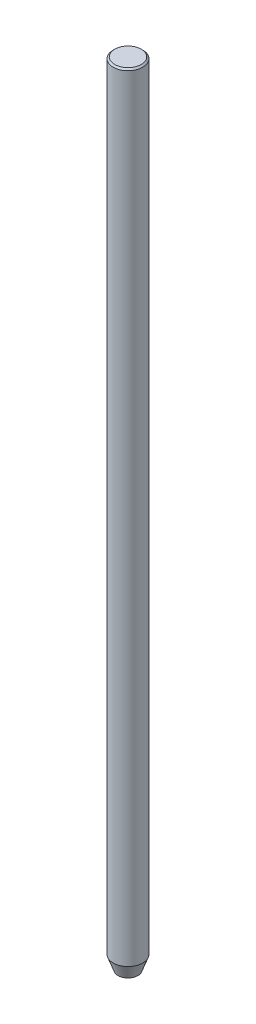
SolidWorks part; units mm, degrees
ref_plane "Front Plane" through (0, 0, 0) normal (0, 0, 1) x (1, 0, 0)
ref_plane "Top Plane" through (0, 0, 0) normal (0, 1, 0) x (1, 0, 0)
ref_plane "Right Plane" through (0, 0, 0) normal (1, 0, 0) x (0, 0, -1)
sketch "Sketch1" plane through (0, 0, 0) normal (0, 1, 0) x (1, 0, 0)
  circle A0 centre (0, 0) radius 2.3812
  dimension "D1" = 4.7625
extrude "Boss-Extrude1" add sketch "Sketch1" along normal blind 127
chamfer "Chamfer1" distance 0.25 angle 45 2 edges at (0, 0, 2.3812) (0, 127, 2.3812)
sketch "Sketch2" plane through (0, 0, 0) normal (1, 0, 0) x (0, 0, -1)
  line L0 (1.6, 0) -> (2.6, 2.7475)
  line L3 (2.6, 2.7475) -> (2.6, 0)
  line L4 (2.6, 0) -> (1.6, 0)
  line L5 (0, 0) -> (0, 2.1784) construction
  line L6 (-2.1313, 0) -> (2.1313, 0) construction
  dimension "D1" = 1
  dimension "D2" = 70
  dimension "D3" = 1.6
revolve "Cut-Revolve1" cut sketch "Sketch2" angle 360 about L5
